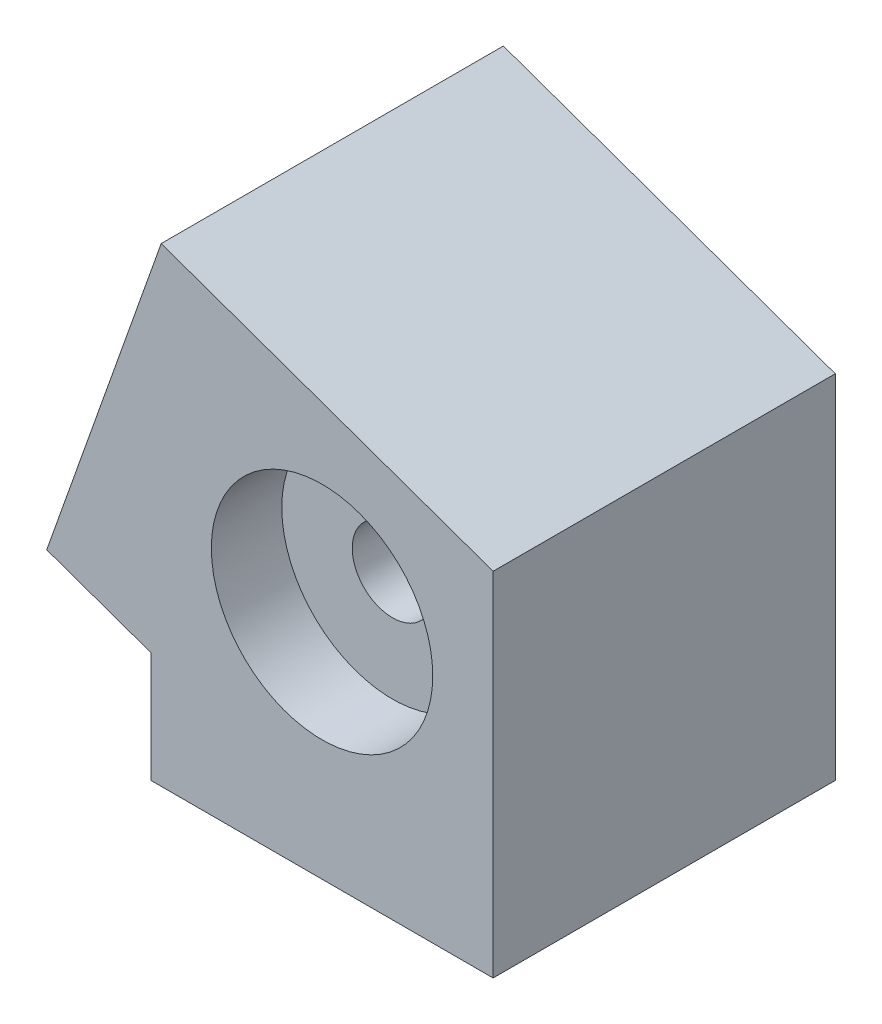
SolidWorks part; units mm, degrees
ref_plane "Front Plane" through (0, 0, 0) normal (0, 0, 1) x (1, 0, 0)
ref_plane "Top Plane" through (0, 0, 0) normal (0, 1, 0) x (1, 0, 0)
ref_plane "Right Plane" through (0, 0, 0) normal (1, 0, 0) x (0, 0, -1)
sketch "Sketch2" plane through (0, 0, 0) normal (0, 1, 0) x (1, 0, 0)
  line L1 (-17, -17) -> (17, -17)
  line L2 (-17, -17) -> (-17, 17)
  line L3 (-17, 17) -> (17, 17)
  line L4 (17, -17) -> (17, 17)
  line L5 (-17, -17) -> (17, 17) construction
  line L6 (-17, 17) -> (17, -17) construction
  line L11 (-15, 15) -> (15, -15) construction
  line L12 (-15, -15) -> (15, 15) construction
  point P0 (0, 0)
  point P7 (0, 0)
  dimension "D1" = 30
  dimension "D2" = 30
extrude "Boss-Extrude2" add sketch "Sketch2" along normal blind 35
sketch "Sketch16" plane through (0, 0, 17) normal (0, 0, 1) x (1, 0, 0)
  line L0 (-17, 35) -> (-17, 10.9918)
  line L1 (-17, 35) -> (-17, 0) construction
  line L2 (-17, 35) -> (17, 35)
  line L3 (17, 35) -> (-17, 10.9918)
extrude "Cut-Extrude6" cut sketch "Sketch16" against normal blind 35
sketch "Sketch17" plane through (0, 0, 0) normal (0, -1, 0) x (1, 0, 0)
  line L1 (-15, -15) -> (15, -15)
  line L2 (-15, -15) -> (-15, 15)
  line L3 (-15, 15) -> (15, 15)
  line L4 (15, -15) -> (15, 15)
  line L5 (-15, -15) -> (15, 15) construction
  line L6 (-15, 15) -> (15, -15) construction
  point P0 (0, 0)
  dimension "D1" = 30
  dimension "D2" = 30
extrude "Cut-Extrude7" cut sketch "Sketch17" against normal blind 10
mirror "Mirror6" about plane through (17, 35, -18) normal (0.5768, -0.8169, 0) of "Cut-Extrude7", "Boss-Extrude2"
sketch "Sketch18" plane through (15, 0, 0) normal (-1, 0, 0) x (0, 0, 1)
  line L1 (-15, 10) -> (15, 10)
  line L2 (-15, 10) -> (-15, 0)
  line L3 (-15, 0) -> (15, 0)
  line L4 (15, 10) -> (15, 0)
extrude "Cut-Extrude8" cut sketch "Sketch18" along normal blind 30
sketch "Sketch19" plane through (0, 0, -17) normal (0, 0, -1) x (-1, 0, 0)
  line L0 (-17, 35) -> (17, 10.9918)
  circle A0 centre (0, 22.9959) radius 11
  dimension "D1" = 22
extrude "Cut-Extrude10" cut sketch "Sketch19" against normal blind 7 contours A0
sketch "Sketch20" plane through (0, 0, 17) normal (0, 0, 1) x (1, 0, 0)
  line L0 (-17, 10.9918) -> (17, 35)
  circle A0 centre (0, 22.9959) radius 11
  dimension "D1" = 22
extrude "Cut-Extrude11" cut sketch "Sketch20" against normal blind 7 contours A0
sketch "Sketch22" plane through (0, 0, 10) normal (0, 0, 1) x (1, 0, 0)
  circle A0 centre (0, 22.9959) radius 4
  circle A1 centre (0, 22.9959) radius 11 construction
  dimension "D1" = 0
  dimension "D2" = 8
extrude "Cut-Extrude12" cut sketch "Sketch22" against normal blind 30
